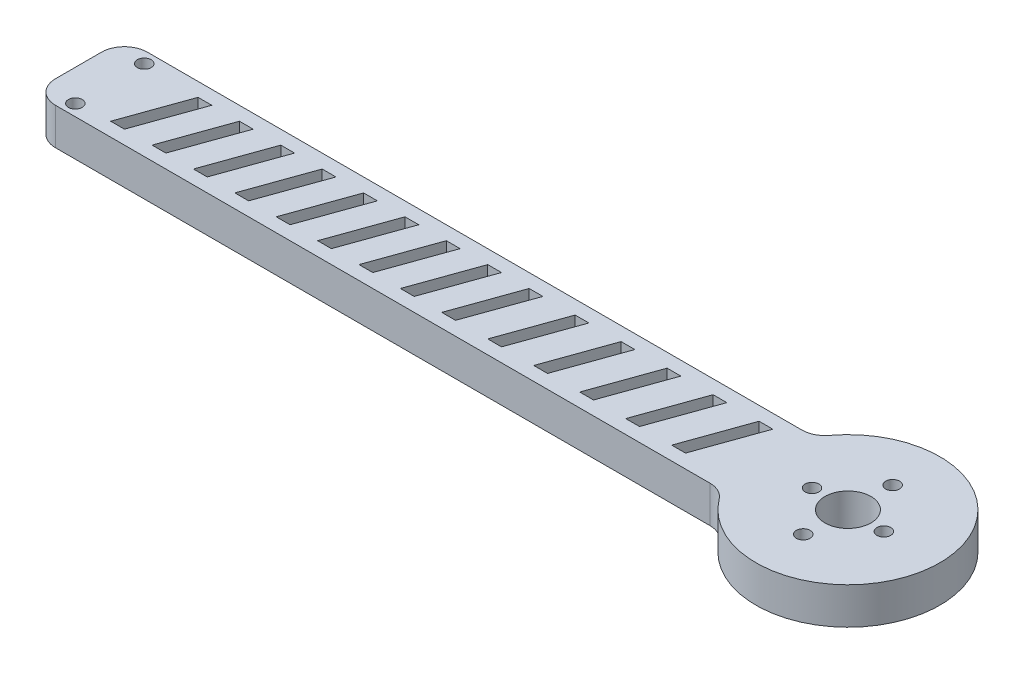
SolidWorks part; units mm, degrees
ref_plane "Front Plane" through (0, 0, 0) normal (0, 0, 1) x (1, 0, 0)
ref_plane "Top Plane" through (0, 0, 0) normal (0, 1, 0) x (1, 0, 0)
ref_plane "Right Plane" through (0, 0, 0) normal (1, 0, 0) x (0, 0, -1)
sketch "Sketch1" plane through (0, 0, 0) normal (0, 1, 0) x (1, 0, 0)
  line L1 (0, 0) -> (150, 0)
  line L2 (0, 0) -> (0, 20)
  line L3 (0, 20) -> (150, 20)
  arc A0 (150, 20) -> (150, 0) centre (167.3205, 10) cw
  dimension "D2" = 20
  dimension "D3" = 20
  dimension "D1" = 150
  dimension "D4" = 17.3205
extrude "Boss-Extrude1" add sketch "Sketch1" along normal blind 8
sketch "Sketch2" plane through (0, 8, 0) normal (0, 1, 0) x (1, 0, 0)
  line L0 (167.5433, 19.4974) -> (167.0977, 0.5026) construction
  line L1 (159.3227, 10.1876) -> (175.3183, 9.8124) construction
  arc A0 (150, 0) -> (150, 20) centre (167.3205, 10) ccw construction
  circle A1 centre (167.3205, 10) radius 9.5 construction
  circle A3 centre (167.0977, 0.5026) radius 1.5
  circle A5 centre (167.5433, 19.4974) radius 1.5
  circle A6 centre (167.3205, 10) radius 8 construction
  circle A7 centre (175.3183, 9.8124) radius 1.5
  circle A8 centre (159.3227, 10.1876) radius 1.5
  circle A9 centre (167.3205, 10) radius 5
  point P0 (167.3205, 10)
  point P14 (130.2079, 19.0506)
  point P17 (140.8207, 0.6191)
  dimension "D1" = 19
  dimension "D2" = 16
  dimension "D4" = 3
  dimension "D5" = 3
  dimension "D6" = 10
  dimension "D3" = 90
  dimension "D7" = 90
extrude "Cut-Extrude1" cut sketch "Sketch2" against normal blind 25
fillet "Fillet1" radius 5 4 edges at (150, 4, -20) (150, 4, 0) (0, 4, -20) (0, 4, 0)
sketch "Sketch4" plane through (0, 8, 0) normal (0, 1, 0) x (1, 0, 0)
  line L0 (96, 3) -> (100.9977, 17)
  line L1 (103.9977, 17) -> (99, 3)
  line L2 (100.9977, 17) -> (103.9977, 17)
  line L6 (147.3205, 17) -> (5, 17)
  line L7 (3, 15) -> (3, 5)
  line L8 (5, 3) -> (147.3205, 3)
  line L9 (147.3205, 17) -> (12.9977, 17) construction
  line L10 (3, 15) -> (3, 5) construction
  line L11 (14, 3) -> (147.3205, 3) construction
  line L13 (21.9977, 17) -> (17, 3)
  line L14 (14, 3) -> (18.9977, 17)
  line L15 (18.9977, 17) -> (21.9977, 17)
  line L16 (17, 3) -> (14, 3)
  line L17 (30.9977, 17) -> (26, 3)
  line L18 (23, 3) -> (27.9977, 17)
  line L19 (27.9977, 17) -> (30.9977, 17)
  line L20 (26, 3) -> (23, 3)
  line L21 (39.9977, 17) -> (35, 3)
  line L22 (32, 3) -> (36.9977, 17)
  line L23 (36.9977, 17) -> (39.9977, 17)
  line L24 (35, 3) -> (32, 3)
  line L25 (48.9977, 17) -> (44, 3)
  line L26 (41, 3) -> (45.9977, 17)
  line L27 (45.9977, 17) -> (48.9977, 17)
  line L28 (44, 3) -> (41, 3)
  line L29 (57.9977, 17) -> (53, 3)
  line L30 (50, 3) -> (54.9977, 17)
  line L31 (54.9977, 17) -> (57.9977, 17)
  line L32 (53, 3) -> (50, 3)
  line L33 (66.9977, 17) -> (62, 3)
  line L34 (59, 3) -> (63.9977, 17)
  line L35 (63.9977, 17) -> (66.9977, 17)
  line L36 (62, 3) -> (59, 3)
  line L37 (75.9977, 17) -> (71, 3)
  line L38 (68, 3) -> (72.9977, 17)
  line L39 (72.9977, 17) -> (75.9977, 17)
  line L40 (71, 3) -> (68, 3)
  line L41 (84.9977, 17) -> (80, 3)
  line L42 (77, 3) -> (81.9977, 17)
  line L43 (81.9977, 17) -> (84.9977, 17)
  line L44 (80, 3) -> (77, 3)
  line L45 (93.9977, 17) -> (89, 3)
  line L46 (86, 3) -> (90.9977, 17)
  line L47 (90.9977, 17) -> (93.9977, 17)
  line L48 (89, 3) -> (86, 3)
  line L49 (9.9977, 17) -> (5, 17) construction
  line L50 (99, 3) -> (96, 3)
  line L51 (106, 3) -> (110.9977, 17)
  line L52 (113.9977, 17) -> (109, 3)
  line L53 (110.9977, 17) -> (113.9977, 17)
  line L54 (109, 3) -> (106, 3)
  line L55 (116, 3) -> (120.9977, 17)
  line L56 (123.9977, 17) -> (119, 3)
  line L57 (120.9977, 17) -> (123.9977, 17)
  line L58 (119, 3) -> (116, 3)
  line L59 (126, 3) -> (130.9977, 17)
  line L60 (133.9977, 17) -> (129, 3)
  line L61 (130.9977, 17) -> (133.9977, 17)
  line L62 (129, 3) -> (126, 3)
  line L63 (136, 3) -> (140.9977, 17)
  line L64 (143.9977, 17) -> (139, 3)
  line L65 (140.9977, 17) -> (143.9977, 17)
  line L66 (139, 3) -> (136, 3)
  arc A10 (5, 17) -> (3, 15) centre (5, 15) ccw
  arc A11 (3, 5) -> (5, 3) centre (5, 5) ccw
  arc A12 (153.7205, -0.2) -> (147.3205, 3) centre (147.3205, -5) ccw
  arc A13 (153.7205, -0.2) -> (153.7205, 20.2) centre (167.3205, 10) ccw
  arc A14 (147.3205, 17) -> (153.7205, 20.2) centre (147.3205, 25) ccw
  arc A15 (5, 17) -> (3, 15) centre (5, 15) ccw construction
  arc A16 (3, 5) -> (5, 3) centre (5, 5) ccw construction
  arc A17 (153.7205, -0.2) -> (147.3205, 3) centre (147.3205, -5) ccw construction
  arc A18 (153.7205, -0.2) -> (153.7205, 20.2) centre (167.3205, 10) ccw construction
  arc A19 (147.3205, 17) -> (153.7205, 20.2) centre (147.3205, 25) ccw construction
  dimension "D2" = 6
  dimension "D1" = 3
extrude "Cut-Extrude2" cut sketch "Sketch4" against normal blind 25
sketch "Sketch5" plane through (0, 8, 0) normal (0, 1, 0) x (1, 0, 0)
  line L0 (6.8101, 2.5) -> (6.8101, 17.5)
  line L1 (0, 15) -> (0, 5) construction
  circle A0 centre (6.8101, 17.5) radius 1.5
  circle A1 centre (6.8101, 2.5) radius 1.5
  point P2 (6.8101, 10)
  point P3 (0, 10)
  dimension "D2" = 3
  dimension "D3" = 3
  dimension "D1" = 15
extrude "Cut-Extrude3" cut sketch "Sketch5" against normal blind 25
